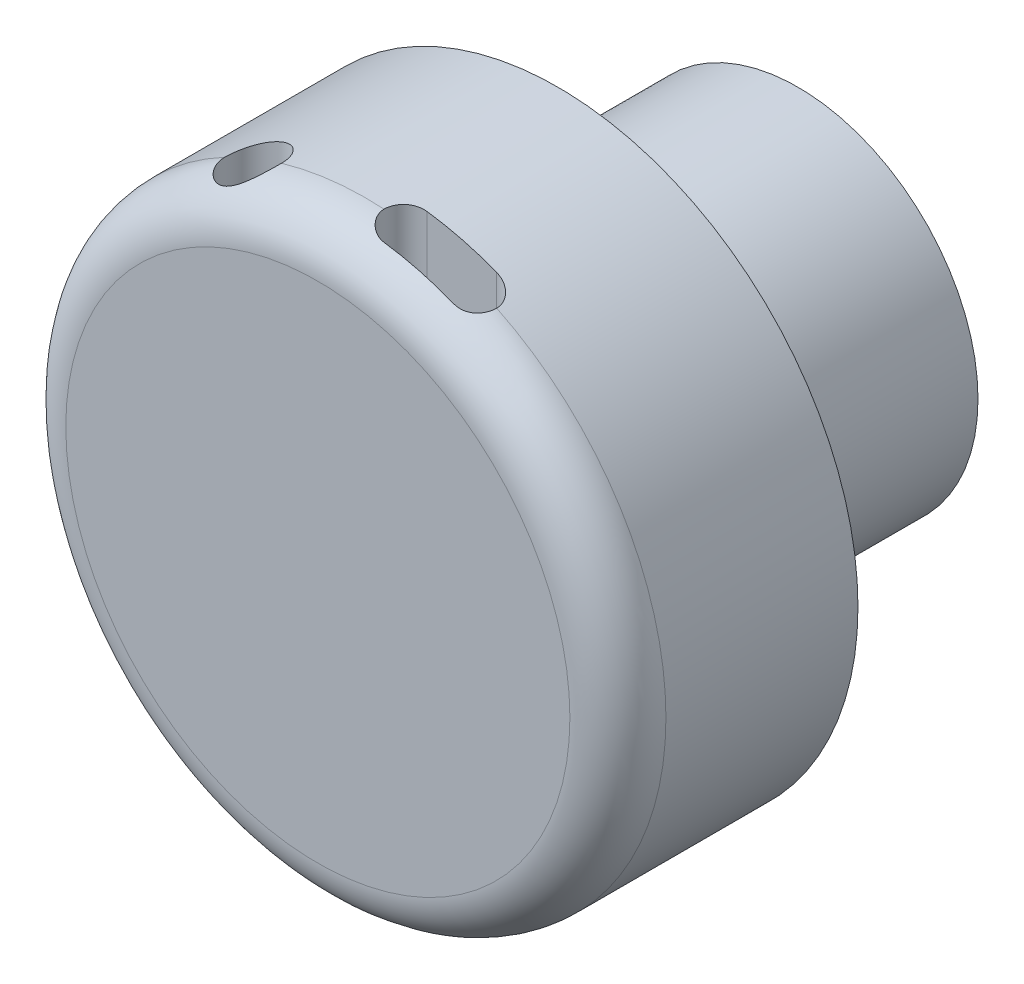
SolidWorks part; units mm, degrees
ref_plane "Front" through (0, 0, 0) normal (0, 0, 1) x (1, 0, 0)
ref_plane "Top" through (0, 0, 0) normal (0, 1, 0) x (1, 0, 0)
ref_plane "Right" through (0, 0, 0) normal (1, 0, 0) x (0, 0, -1)
sketch "Sketch1" plane through (0, 0, 0) normal (0, 0, 1) x (1, 0, 0)
  circle A0 centre (0, 0) radius 125
  dimension "D1" = 250
extrude "Boss-Extrude1" add sketch "Sketch1" along normal blind 100
fillet "Fillet1" radius 20 1 edges at (125, 0, 100)
sketch "Sketch2" plane through (0, 0, 0) normal (0, 1, 0) x (1, 0, 0)
  line L0 (125, -80) -> (-125, -80) construction
  line L1 (16.5473, -80) -> (45.5207, -80) construction
  line L2 (16.5473, -71.0227) -> (45.5207, -71.0227)
  line L3 (16.5473, -88.9773) -> (45.5207, -88.9773)
  circle A0 centre (-46.9508, -80) radius 11.8058
  arc A1 (16.5473, -71.0227) -> (16.5473, -88.9773) centre (16.5473, -80) ccw
  arc A2 (45.5207, -88.9773) -> (45.5207, -71.0227) centre (45.5207, -80) ccw
  point P6 (31.034, -80)
extrude "Cut-Extrude1" cut sketch "Sketch2" against normal through all both and the other way through all
sketch "Sketch3" plane through (0, 0, 0) normal (0, 0, -1) x (-1, 0, 0)
  circle A0 centre (0, 0) radius 75
  dimension "D1" = 150
extrude "Boss-Extrude2" add sketch "Sketch3" along normal blind 100
chamfer "Chamfer1" distance 28.26 angle 31 1 edges at (-75, 0, 0)
